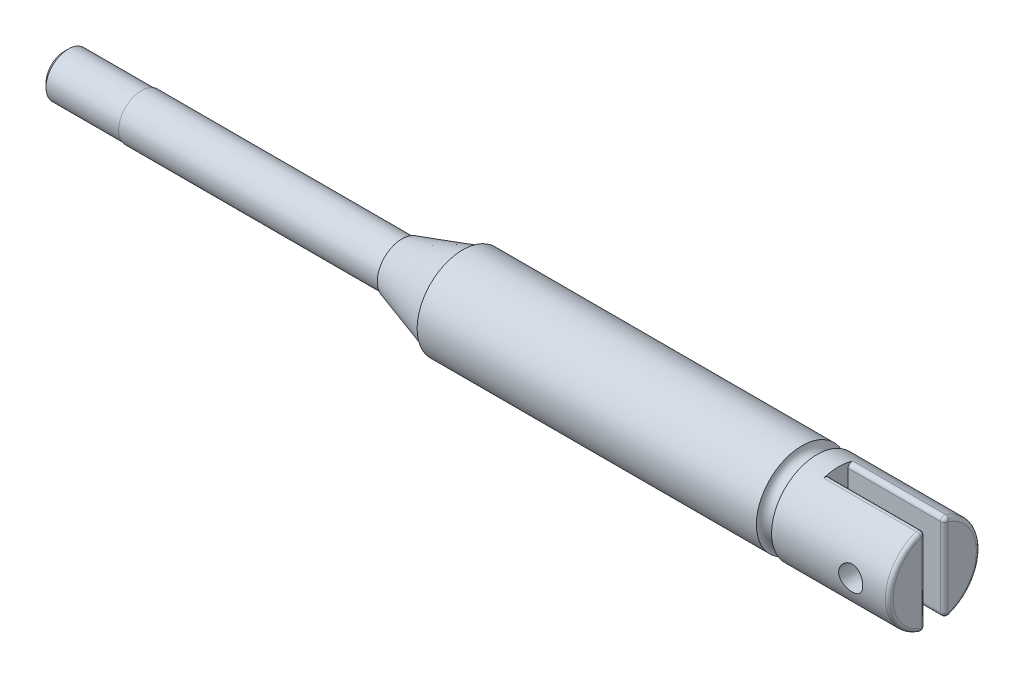
SolidWorks part; units mm, degrees
ref_plane "Plan de face" through (0, 0, 0) normal (0, 0, 1) x (1, 0, 0)
ref_plane "Plan de dessus" through (0, 0, 0) normal (0, 1, 0) x (1, 0, 0)
ref_plane "Plan de droite" through (0, 0, 0) normal (1, 0, 0) x (0, 0, -1)
sketch "Esquisse1" plane through (0, 0, 0) normal (0, 0, 1) x (1, 0, 0)
  line L0 (-76.0313, 0) -> (76.0313, 0) construction
  line L2 (0, 0) -> (0, 3)
  line L3 (0, 3) -> (-31.115, 3)
  line L4 (-31.115, 3) -> (-31.115, 2.873)
  line L5 (-31.115, 2.873) -> (-35.115, 1.627)
  line L6 (-35.115, 1.627) -> (-35.115, 1.5)
  line L7 (-35.115, 1.5) -> (-57.3684, 1.5)
  line L8 (0, 0) -> (-57.3684, 0)
  line L9 (-57.3684, 0) -> (-57.3684, 1.5)
  dimension "D1" = 3
  dimension "D2" = 6
  dimension "D3" = 4
  dimension "D4" = 0.127
  dimension "D5" = 31.115
  dimension "D6" = 57.3684
revolve "Révolution1" add sketch "Esquisse1" angle 360 about L0
sketch "Esquisse2" plane through (0, 0, 0) normal (0, 1, 0) x (1, 0, 0)
  line L0 (0, -3.3) -> (0, 3.3) construction
  line L1 (-6.35, -0.635) -> (6.35, -0.635)
  line L2 (-6.35, -0.635) -> (-6.35, 0.635)
  line L3 (-6.35, 0.635) -> (6.35, 0.635)
  line L4 (6.35, -0.635) -> (6.35, 0.635)
  line L5 (-6.35, -0.635) -> (6.35, 0.635) construction
  line L6 (-6.35, 0.635) -> (6.35, -0.635) construction
  point P0 (0, 0)
  dimension "D1" = 1.27
  dimension "D2" = 6.35
extrude "Enlèv. mat.-Extru.1" cut sketch "Esquisse2" against normal through all both and the other way through all
sketch "Esquisse3" plane through (0, 0, 0) normal (0, 0, 1) x (1, 0, 0)
  line L0 (3.3, 0) -> (-3.3, 0) construction
  line L1 (0, -3.3) -> (0, 3.3) construction
  circle A0 centre (-2.54, 0) radius 0.7938
  dimension "D1" = 1.5875
  dimension "D2" = 2.54
extrude "Enlèv. mat.-Extru.2" cut sketch "Esquisse3" against normal through all both and the other way through all
sketch "Esquisse4" plane through (0, 0, 0) normal (0, 0, 1) x (1, 0, 0)
  line L0 (-57.3684, 1.4605) -> (-57.3684, 1.5)
  line L1 (-57.3684, 1.5) -> (-57.3684, -1.5) construction
  line L2 (-57.3684, 1.5) -> (-52.2884, 1.5)
  line L3 (-35.115, 1.5) -> (-57.3684, 1.5) construction
  line L4 (-52.2884, 1.5) -> (-52.2884, 1.4605)
  line L5 (-52.2884, 1.4605) -> (-57.3684, 1.4605)
  line L6 (-57.3684, 1.4605) -> (-58.8283, 1.439)
  line L8 (-63.4331, 0) -> (63.4331, 0) construction
  dimension "D1" = 2.921
  dimension "D2" = 5.08
revolve "Enlèvement de matière-Révolution1" cut sketch "Esquisse4" angle 360 about L8
chamfer "Chanfrein1" distance 0.254 angle 45 1 edges at (-57.3684, -1.4605, 0)
fillet "Congé1" radius 0.254 8 edges at (0, 0, -0.635) (0, 0, -3) (0, 0, 0.635) (0, 0, 3) (-3.175, 2.932, -0.635) (-3.175, -2.932, -0.635) (-3.175, 2.932, 0.635) (-3.175, -2.932, 0.635)
sketch "Esquisse5" plane through (0, 0, 0) normal (0, 0, 1) x (1, 0, 0)
  line L0 (-6.35, 3) -> (-31.115, 3) construction
  line L1 (0, -3.3) -> (0, 3.3) construction
  circle A0 centre (-8.255, 3) radius 0.5
  dimension "D1" = 1
  dimension "D2" = 8.255
revolve "Enlèvement de matière-Révolution2" cut sketch "Esquisse5" angle 360 about axis through (-76.0313, 0, 0) along (-1, 0, 0)
